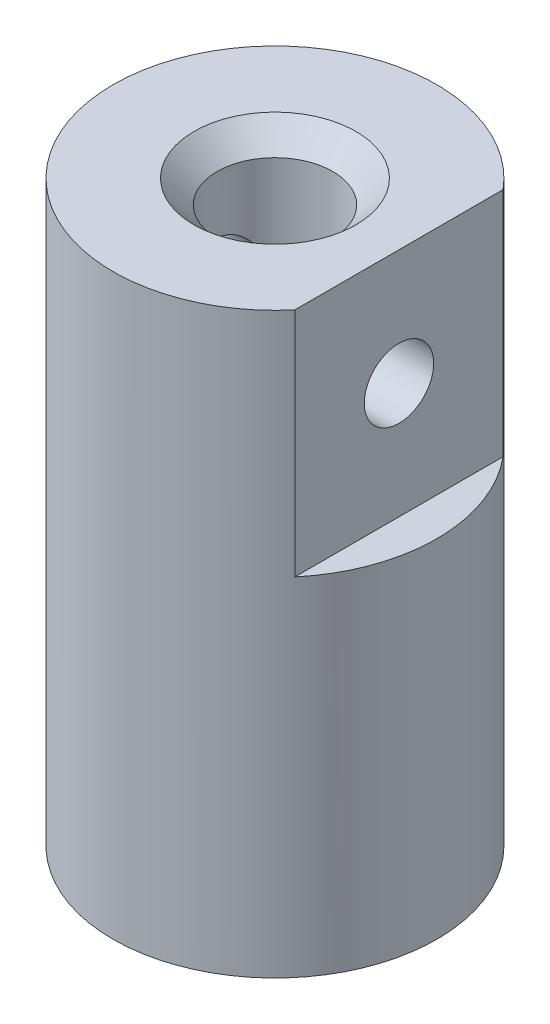
SolidWorks part; units mm, degrees
ref_plane "Plan de face" through (0, 0, 0) normal (0, 0, 1) x (1, 0, 0)
ref_plane "Plan de dessus" through (0, 0, 0) normal (0, 1, 0) x (1, 0, 0)
ref_plane "Plan de droite" through (0, 0, 0) normal (1, 0, 0) x (0, 0, -1)
sketch "Esquisse1" plane through (0, 0, 0) normal (0, 1, 0) x (1, 0, 0)
  circle A0 centre (0, 0) radius 7
  dimension "D1" = 14
extrude "Boss.-Extru.1" add sketch "Esquisse1" along normal blind 25
sketch "Esquisse2" plane through (0, 0, 0) normal (0, -1, 0) x (-1, 0, 0)
  circle A0 centre (0, 0) radius 2.5
  dimension "D1" = 5
extrude "Enlèv. mat.-Extru.1" cut sketch "Esquisse2" against normal up to next
chamfer "Chanfrein1" distance 0.5 angle 45 1 edges at (0, 0, -2.5)
chamfer "Chanfrein2" distance 1 angle 45 1 edges at (0, 25, 2.5)
sketch "Esquisse3" plane through (0, 25, 0) normal (0, 1, 0) x (1, 0, 0)
  line L0 (0, 0) -> (7, 0) construction
  line L1 (5.3619, 4.5) -> (5.3619, -4.5)
  circle A0 centre (0, 0) radius 7 construction
  circle A1 centre (0, 0) radius 7
  circle M3 centre (0, 0) radius 7
  dimension "D1" = 9
extrude "Enlèv. mat.-Extru.2" cut sketch "Esquisse3" against normal blind 10 contours L0 L1 M3 | L1 L0 A1
sketch "Esquisse4" plane through (5.3619, 0, 0) normal (1, 0, 0) x (0, 0, -1)
  line L0 (0, 25) -> (0, 15) construction
  line L1 (4.5, 25) -> (-4.5, 25) construction
  line L2 (4.5, 15) -> (-4.5, 15) construction
  circle A0 centre (0, 20) radius 1.5
  dimension "D1" = 3
extrude "Enlèv. mat.-Extru.3" cut sketch "Esquisse4" against normal through all
